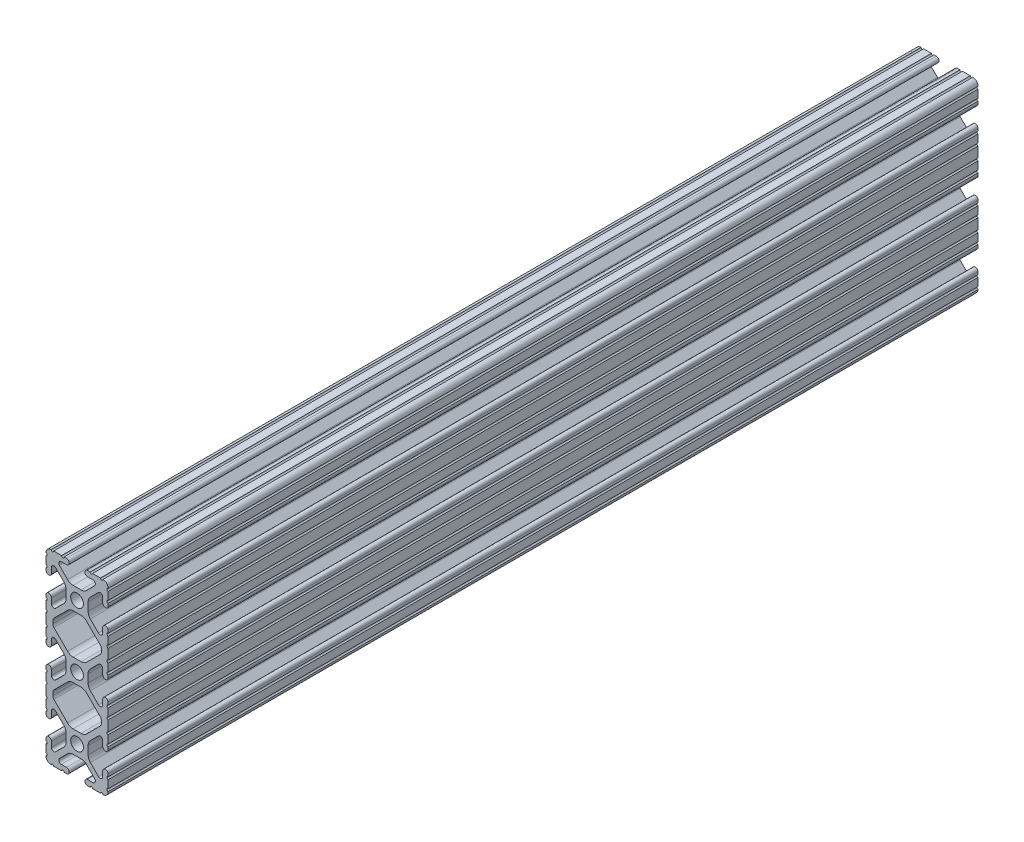
SolidWorks part; units mm, degrees
ref_plane "Front" through (0, 0, 0) normal (0, 0, 1) x (1, 0, 0)
ref_plane "Top" through (0, 0, 0) normal (0, 1, 0) x (1, 0, 0)
ref_plane "Right" through (0, 0, 0) normal (1, 0, 0) x (0, 0, -1)
sketch "Sketch1" plane through (0, 0, 0) normal (0, 0, 1) x (1, 0, 0)
  line L0 (-7.4908, -34.8742) -> (7.4908, -34.8742) construction
  line L1 (-3.1974, -36.9951) -> (3.1974, -36.9951) construction
  line L2 (-7.4908, 34.8742) -> (7.4908, 34.8742) construction
  line L3 (-3.1974, 36.9951) -> (3.1974, 36.9951) construction
  line L16 (-9.9314, -12.1463) -> (-9.9314, -13.2537)
  line L17 (-3.8759, -5.4384) -> (-9.4702, -11.0327)
  line L18 (1.6308, -4.5085) -> (-1.6308, -4.5085)
  line L19 (9.4702, -11.0327) -> (3.8759, -5.4384)
  line L20 (9.9314, -13.2537) -> (9.9314, -12.1463)
  line L21 (3.8759, -19.9616) -> (9.4702, -14.3673)
  line L22 (-1.6308, -20.8915) -> (1.6308, -20.8915)
  line L23 (-9.4702, -14.3673) -> (-3.8759, -19.9616)
  line L32 (-9.9314, 13.2537) -> (-9.9314, 12.1463)
  line L33 (-3.8759, 19.9616) -> (-9.4702, 14.3673)
  line L34 (1.6308, 20.8915) -> (-1.6308, 20.8915)
  line L35 (9.4702, 14.3673) -> (3.8759, 19.9616)
  line L36 (9.9314, 12.1463) -> (9.9314, 13.2537)
  line L37 (3.8759, 5.4384) -> (9.4702, 11.0327)
  line L38 (-1.6308, 4.5085) -> (1.6308, 4.5085)
  line L39 (-9.4702, 11.0327) -> (-3.8759, 5.4384)
  line L152 (-12.7, 34.9504) -> (-12.7, 31.7246)
  line L153 (-12.7, 30.7086) -> (-12.7, 29.7023)
  line L154 (-10.4902, 29.7023) -> (-10.4902, 31.8748)
  line L155 (-8.7558, 32.5932) -> (-5.4384, 29.2759)
  line L156 (-4.5085, 27.0308) -> (-4.5085, 23.7692)
  line L157 (-5.4384, 21.5241) -> (-8.7558, 18.2068)
  line L158 (-10.4902, 18.9252) -> (-10.4902, 21.0977)
  line L159 (-12.7, 21.0977) -> (-12.7, 20.0914)
  line L160 (-12.7, 19.0754) -> (-12.7, 15.8496)
  line L161 (-12.7, 14.8336) -> (-12.7, 10.5664)
  line L162 (-12.7, 9.5504) -> (-12.7, 6.3246)
  line L163 (-12.7, 5.3086) -> (-12.7, 4.3023)
  line L164 (-10.4902, 4.3023) -> (-10.4902, 6.4748)
  line L165 (-8.7558, 7.1932) -> (-5.4384, 3.8759)
  line L166 (-4.5085, 1.6308) -> (-4.5085, -1.6308)
  line L167 (-5.4384, -3.8759) -> (-8.7558, -7.1932)
  line L168 (-10.4902, -6.4748) -> (-10.4902, -4.3023)
  line L169 (-12.7, -4.3023) -> (-12.7, -5.3086)
  line L170 (-12.7, -6.3246) -> (-12.7, -9.5504)
  line L171 (-12.7, -10.5664) -> (-12.7, -14.8336)
  line L172 (-12.7, -15.8496) -> (-12.7, -19.0754)
  line L173 (-12.7, -20.0914) -> (-12.7, -21.0977)
  line L174 (-10.4902, -21.0977) -> (-10.4902, -18.9252)
  line L175 (-8.7558, -18.2068) -> (-5.4384, -21.5241)
  line L176 (-4.5085, -23.7692) -> (-4.5085, -27.0308)
  line L177 (-5.4384, -29.2759) -> (-8.7558, -32.5932)
  line L178 (-10.4902, -31.8748) -> (-10.4902, -29.7023)
  line L179 (-12.7, -29.7023) -> (-12.7, -30.7086)
  line L180 (-12.7, -31.7246) -> (-12.7, -34.9504)
  line L181 (-9.5504, -38.1) -> (-6.3246, -38.1)
  line L182 (-5.3086, -38.1) -> (-4.3023, -38.1)
  line L183 (-4.3023, -35.8902) -> (-6.4748, -35.8902)
  line L184 (-7.1932, -34.1558) -> (-3.8759, -30.8384)
  line L185 (-1.6308, -29.9085) -> (1.6308, -29.9085)
  line L186 (3.8759, -30.8384) -> (7.1932, -34.1558)
  line L187 (6.4748, -35.8902) -> (4.3023, -35.8902)
  line L188 (4.3023, -38.1) -> (5.3086, -38.1)
  line L189 (6.3246, -38.1) -> (9.5504, -38.1)
  line L190 (12.7, -34.9504) -> (12.7, -31.7246)
  line L191 (12.7, -30.7086) -> (12.7, -29.7023)
  line L192 (10.4902, -29.7023) -> (10.4902, -31.8748)
  line L193 (8.7558, -32.5932) -> (5.4384, -29.2759)
  line L194 (4.5085, -27.0308) -> (4.5085, -23.7692)
  line L195 (5.4384, -21.5241) -> (8.7558, -18.2068)
  line L196 (10.4902, -18.9252) -> (10.4902, -21.0977)
  line L197 (12.7, -21.0977) -> (12.7, -20.0914)
  line L198 (12.7, -19.0754) -> (12.7, -15.8496)
  line L199 (12.7, -14.8336) -> (12.7, -10.5664)
  line L200 (12.7, -9.5504) -> (12.7, -6.3246)
  line L201 (12.7, -5.3086) -> (12.7, -4.3023)
  line L202 (10.4902, -4.3023) -> (10.4902, -6.4748)
  line L203 (8.7558, -7.1932) -> (5.4384, -3.8759)
  line L204 (4.5085, -1.6308) -> (4.5085, 1.6308)
  line L205 (5.4384, 3.8759) -> (8.7558, 7.1932)
  line L206 (10.4902, 6.4748) -> (10.4902, 4.3023)
  line L207 (12.7, 4.3023) -> (12.7, 5.3086)
  line L208 (12.7, 6.3246) -> (12.7, 9.5504)
  line L209 (12.7, 10.5664) -> (12.7, 14.8336)
  line L210 (12.7, 15.8496) -> (12.7, 19.0754)
  line L211 (12.7, 20.0914) -> (12.7, 21.0977)
  line L212 (10.4902, 21.0977) -> (10.4902, 18.9252)
  line L213 (8.7558, 18.2068) -> (5.4384, 21.5241)
  line L214 (4.5085, 23.7692) -> (4.5085, 27.0308)
  line L215 (5.4384, 29.2759) -> (8.7558, 32.5932)
  line L216 (10.4902, 31.8748) -> (10.4902, 29.7023)
  line L217 (12.7, 29.7023) -> (12.7, 30.7086)
  line L218 (12.7, 31.7246) -> (12.7, 34.9504)
  line L219 (9.5504, 38.1) -> (6.3246, 38.1)
  line L220 (5.3086, 38.1) -> (4.3023, 38.1)
  line L221 (4.3023, 35.8902) -> (6.4748, 35.8902)
  line L222 (7.1932, 34.1558) -> (3.8759, 30.8384)
  line L223 (1.6308, 29.9085) -> (-1.6308, 29.9085)
  line L224 (-3.8759, 30.8384) -> (-7.1932, 34.1558)
  line L225 (-6.4748, 35.8902) -> (-4.3023, 35.8902)
  line L226 (-4.3023, 38.1) -> (-5.3086, 38.1)
  line L227 (-6.3246, 38.1) -> (-9.5504, 38.1)
  circle A2 centre (0, -25.4) radius 2.6035
  circle A4 centre (0, 0) radius 2.6035
  circle A6 centre (0, 25.4) radius 2.6035
  arc A18 (-9.9314, -13.2537) -> (-9.4702, -14.3673) centre (-8.3566, -13.2537) ccw
  arc A19 (-9.4702, -11.0327) -> (-9.9314, -12.1463) centre (-8.3566, -12.1463) ccw
  arc A20 (-1.6308, -4.5085) -> (-3.8759, -5.4384) centre (-1.6308, -7.6835) ccw
  arc A21 (3.8759, -5.4384) -> (1.6308, -4.5085) centre (1.6308, -7.6835) ccw
  arc A22 (9.9314, -12.1463) -> (9.4702, -11.0327) centre (8.3566, -12.1463) ccw
  arc A23 (9.4702, -14.3673) -> (9.9314, -13.2537) centre (8.3566, -13.2537) ccw
  arc A24 (1.6308, -20.8915) -> (3.8759, -19.9616) centre (1.6308, -17.7165) ccw
  arc A25 (-3.8759, -19.9616) -> (-1.6308, -20.8915) centre (-1.6308, -17.7165) ccw
  arc A36 (-9.9314, 12.1463) -> (-9.4702, 11.0327) centre (-8.3566, 12.1463) ccw
  arc A37 (-9.4702, 14.3673) -> (-9.9314, 13.2537) centre (-8.3566, 13.2537) ccw
  arc A38 (-1.6308, 20.8915) -> (-3.8759, 19.9616) centre (-1.6308, 17.7165) ccw
  arc A39 (3.8759, 19.9616) -> (1.6308, 20.8915) centre (1.6308, 17.7165) ccw
  arc A40 (9.9314, 13.2537) -> (9.4702, 14.3673) centre (8.3566, 13.2537) ccw
  arc A41 (9.4702, 11.0327) -> (9.9314, 12.1463) centre (8.3566, 12.1463) ccw
  arc A42 (1.6308, 4.5085) -> (3.8759, 5.4384) centre (1.6308, 7.6835) ccw
  arc A43 (-3.8759, 5.4384) -> (-1.6308, 4.5085) centre (-1.6308, 7.6835) ccw
  arc A168 (-10.5664, 38.1) -> (-12.7, 35.9664) centre (-10.592, 35.992) ccw
  arc A169 (-12.7, 34.9504) -> (-12.7, 35.9664) centre (-12.7, 35.4584) ccw
  arc A170 (-12.7, 30.7086) -> (-12.7, 31.7246) centre (-12.7, 31.2166) ccw
  arc A171 (-12.7, 29.7023) -> (-10.4902, 29.7023) centre (-11.5951, 29.7023) ccw
  arc A172 (-8.7558, 32.5932) -> (-10.4902, 31.8748) centre (-9.4742, 31.8748) ccw
  arc A173 (-4.5085, 27.0308) -> (-5.4384, 29.2759) centre (-7.6835, 27.0308) ccw
  arc A174 (-5.4384, 21.5241) -> (-4.5085, 23.7692) centre (-7.6835, 23.7692) ccw
  arc A175 (-10.4902, 18.9252) -> (-8.7558, 18.2068) centre (-9.4742, 18.9252) ccw
  arc A176 (-10.4902, 21.0977) -> (-12.7, 21.0977) centre (-11.5951, 21.0977) ccw
  arc A177 (-12.7, 19.0754) -> (-12.7, 20.0914) centre (-12.7, 19.5834) ccw
  arc A178 (-12.7, 14.8336) -> (-12.7, 15.8496) centre (-12.7, 15.3416) ccw
  arc A179 (-12.7, 9.5504) -> (-12.7, 10.5664) centre (-12.7, 10.0584) ccw
  arc A180 (-12.7, 5.3086) -> (-12.7, 6.3246) centre (-12.7, 5.8166) ccw
  arc A181 (-12.7, 4.3023) -> (-10.4902, 4.3023) centre (-11.5951, 4.3023) ccw
  arc A182 (-8.7558, 7.1932) -> (-10.4902, 6.4748) centre (-9.4742, 6.4748) ccw
  arc A183 (-4.5085, 1.6308) -> (-5.4384, 3.8759) centre (-7.6835, 1.6308) ccw
  arc A184 (-5.4384, -3.8759) -> (-4.5085, -1.6308) centre (-7.6835, -1.6308) ccw
  arc A185 (-10.4902, -6.4748) -> (-8.7558, -7.1932) centre (-9.4742, -6.4748) ccw
  arc A186 (-10.4902, -4.3023) -> (-12.7, -4.3023) centre (-11.5951, -4.3023) ccw
  arc A187 (-12.7, -6.3246) -> (-12.7, -5.3086) centre (-12.7, -5.8166) ccw
  arc A188 (-12.7, -10.5664) -> (-12.7, -9.5504) centre (-12.7, -10.0584) ccw
  arc A189 (-12.7, -15.8496) -> (-12.7, -14.8336) centre (-12.7, -15.3416) ccw
  arc A190 (-12.7, -20.0914) -> (-12.7, -19.0754) centre (-12.7, -19.5834) ccw
  arc A191 (-12.7, -21.0977) -> (-10.4902, -21.0977) centre (-11.5951, -21.0977) ccw
  arc A192 (-8.7558, -18.2068) -> (-10.4902, -18.9252) centre (-9.4742, -18.9252) ccw
  arc A193 (-4.5085, -23.7692) -> (-5.4384, -21.5241) centre (-7.6835, -23.7692) ccw
  arc A194 (-5.4384, -29.2759) -> (-4.5085, -27.0308) centre (-7.6835, -27.0308) ccw
  arc A195 (-10.4902, -31.8748) -> (-8.7558, -32.5932) centre (-9.4742, -31.8748) ccw
  arc A196 (-10.4902, -29.7023) -> (-12.7, -29.7023) centre (-11.5951, -29.7023) ccw
  arc A197 (-12.7, -31.7246) -> (-12.7, -30.7086) centre (-12.7, -31.2166) ccw
  arc A198 (-12.7, -35.9664) -> (-12.7, -34.9504) centre (-12.7, -35.4584) ccw
  arc A199 (-12.7, -35.9664) -> (-10.5664, -38.1) centre (-10.592, -35.992) ccw
  arc A200 (-9.5504, -38.1) -> (-10.5664, -38.1) centre (-10.0584, -38.1) ccw
  arc A201 (-5.3086, -38.1) -> (-6.3246, -38.1) centre (-5.8166, -38.1) ccw
  arc A202 (-4.3023, -38.1) -> (-4.3023, -35.8902) centre (-4.3023, -36.9951) ccw
  arc A203 (-7.1932, -34.1558) -> (-6.4748, -35.8902) centre (-6.4748, -34.8742) ccw
  arc A204 (-1.6308, -29.9085) -> (-3.8759, -30.8384) centre (-1.6308, -33.0835) ccw
  arc A205 (3.8759, -30.8384) -> (1.6308, -29.9085) centre (1.6308, -33.0835) ccw
  arc A206 (6.4748, -35.8902) -> (7.1932, -34.1558) centre (6.4748, -34.8742) ccw
  arc A207 (4.3023, -35.8902) -> (4.3023, -38.1) centre (4.3023, -36.9951) ccw
  arc A208 (6.3246, -38.1) -> (5.3086, -38.1) centre (5.8166, -38.1) ccw
  arc A209 (10.5664, -38.1) -> (9.5504, -38.1) centre (10.0584, -38.1) ccw
  arc A210 (10.5664, -38.1) -> (12.7, -35.9664) centre (10.592, -35.992) ccw
  arc A211 (12.7, -34.9504) -> (12.7, -35.9664) centre (12.7, -35.4584) ccw
  arc A212 (12.7, -30.7086) -> (12.7, -31.7246) centre (12.7, -31.2166) ccw
  arc A213 (12.7, -29.7023) -> (10.4902, -29.7023) centre (11.5951, -29.7023) ccw
  arc A214 (8.7558, -32.5932) -> (10.4902, -31.8748) centre (9.4742, -31.8748) ccw
  arc A215 (4.5085, -27.0308) -> (5.4384, -29.2759) centre (7.6835, -27.0308) ccw
  arc A216 (5.4384, -21.5241) -> (4.5085, -23.7692) centre (7.6835, -23.7692) ccw
  arc A217 (10.4902, -18.9252) -> (8.7558, -18.2068) centre (9.4742, -18.9252) ccw
  arc A218 (10.4902, -21.0977) -> (12.7, -21.0977) centre (11.5951, -21.0977) ccw
  arc A219 (12.7, -19.0754) -> (12.7, -20.0914) centre (12.7, -19.5834) ccw
  arc A220 (12.7, -14.8336) -> (12.7, -15.8496) centre (12.7, -15.3416) ccw
  arc A221 (12.7, -9.5504) -> (12.7, -10.5664) centre (12.7, -10.0584) ccw
  arc A222 (12.7, -5.3086) -> (12.7, -6.3246) centre (12.7, -5.8166) ccw
  arc A223 (12.7, -4.3023) -> (10.4902, -4.3023) centre (11.5951, -4.3023) ccw
  arc A224 (8.7558, -7.1932) -> (10.4902, -6.4748) centre (9.4742, -6.4748) ccw
  arc A225 (4.5085, -1.6308) -> (5.4384, -3.8759) centre (7.6835, -1.6308) ccw
  arc A226 (5.4384, 3.8759) -> (4.5085, 1.6308) centre (7.6835, 1.6308) ccw
  arc A227 (10.4902, 6.4748) -> (8.7558, 7.1932) centre (9.4742, 6.4748) ccw
  arc A228 (10.4902, 4.3023) -> (12.7, 4.3023) centre (11.5951, 4.3023) ccw
  arc A229 (12.7, 6.3246) -> (12.7, 5.3086) centre (12.7, 5.8166) ccw
  arc A230 (12.7, 10.5664) -> (12.7, 9.5504) centre (12.7, 10.0584) ccw
  arc A231 (12.7, 15.8496) -> (12.7, 14.8336) centre (12.7, 15.3416) ccw
  arc A232 (12.7, 20.0914) -> (12.7, 19.0754) centre (12.7, 19.5834) ccw
  arc A233 (12.7, 21.0977) -> (10.4902, 21.0977) centre (11.5951, 21.0977) ccw
  arc A234 (8.7558, 18.2068) -> (10.4902, 18.9252) centre (9.4742, 18.9252) ccw
  arc A235 (4.5085, 23.7692) -> (5.4384, 21.5241) centre (7.6835, 23.7692) ccw
  arc A236 (5.4384, 29.2759) -> (4.5085, 27.0308) centre (7.6835, 27.0308) ccw
  arc A237 (10.4902, 31.8748) -> (8.7558, 32.5932) centre (9.4742, 31.8748) ccw
  arc A238 (10.4902, 29.7023) -> (12.7, 29.7023) centre (11.5951, 29.7023) ccw
  arc A239 (12.7, 31.7246) -> (12.7, 30.7086) centre (12.7, 31.2166) ccw
  arc A240 (12.7, 35.9664) -> (12.7, 34.9504) centre (12.7, 35.4584) ccw
  arc A241 (12.7, 35.9664) -> (10.5664, 38.1) centre (10.592, 35.992) ccw
  arc A242 (9.5504, 38.1) -> (10.5664, 38.1) centre (10.0584, 38.1) ccw
  arc A243 (5.3086, 38.1) -> (6.3246, 38.1) centre (5.8166, 38.1) ccw
  arc A244 (4.3023, 38.1) -> (4.3023, 35.8902) centre (4.3023, 36.9951) ccw
  arc A245 (7.1932, 34.1558) -> (6.4748, 35.8902) centre (6.4748, 34.8742) ccw
  arc A246 (1.6308, 29.9085) -> (3.8759, 30.8384) centre (1.6308, 33.0835) ccw
  arc A247 (-3.8759, 30.8384) -> (-1.6308, 29.9085) centre (-1.6308, 33.0835) ccw
  arc A248 (-6.4748, 35.8902) -> (-7.1932, 34.1558) centre (-6.4748, 34.8742) ccw
  arc A249 (-4.3023, 35.8902) -> (-4.3023, 38.1) centre (-4.3023, 36.9951) ccw
  arc A250 (-6.3246, 38.1) -> (-5.3086, 38.1) centre (-5.8166, 38.1) ccw
  arc A251 (-10.5664, 38.1) -> (-9.5504, 38.1) centre (-10.0584, 38.1) ccw
extrude "Boss-Extrude1" add sketch "Sketch1" along normal mid plane 355.6
